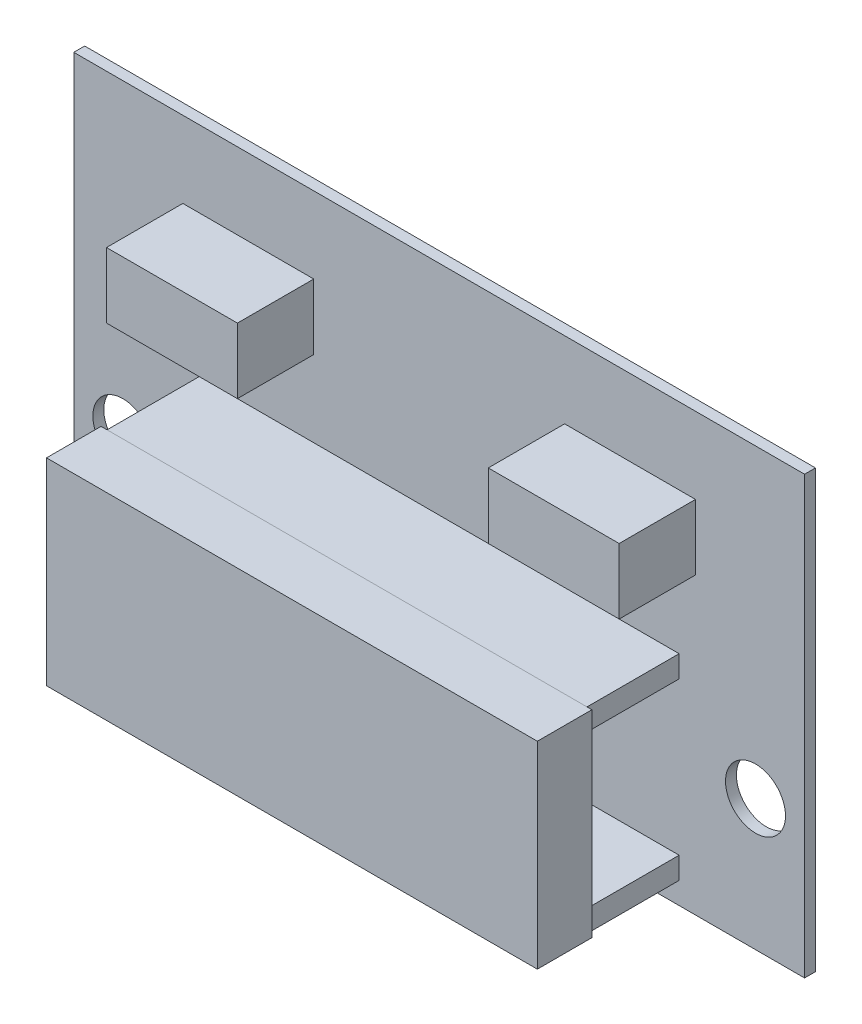
SolidWorks part; units mm, degrees
ref_plane "正面" through (0, 0, 0) normal (0, 0, 1) x (1, 0, 0)
ref_plane "平面" through (0, 0, 0) normal (0, 1, 0) x (1, 0, 0)
ref_plane "右側面" through (0, 0, 0) normal (1, 0, 0) x (0, 0, -1)
ref_plane "平面1" through (0, 0, 0) normal (0, 0, 1) x (1, 0, 0)
sketch "ｽｹｯﾁ1" plane through (0, 0, 0) normal (0, 0, 1) x (1, 0, 0)
  line L1 (-33.5, 20) -> (33.5, 20)
  line L2 (-33.5, 20) -> (-33.5, -20)
  line L3 (-33.5, -20) -> (33.5, -20)
  line L4 (33.5, 20) -> (33.5, -20)
  line L5 (-33.5, 20) -> (33.5, -20) construction
  line L6 (-33.5, -20) -> (33.5, 20) construction
  point P0 (0, 0)
  dimension "D1" = 40
  dimension "D2" = 67
extrude "ﾎﾞｽ - 押し出し1" add sketch "ｽｹｯﾁ1" along normal blind 1
sketch "ｽｹｯﾁ2" plane through (0, 0, 1) normal (0, 0, 1) x (1, 0, 0)
  line L1 (-22, 0) -> (22, 0)
  line L2 (-22, 0) -> (-22, -2)
  line L3 (-22, -2) -> (22, -2)
  line L4 (22, 0) -> (22, -2)
  line L5 (-22, 0) -> (22, -2) construction
  line L6 (-22, -2) -> (22, 0) construction
  line L7 (-22, -16) -> (22, -16)
  line L8 (-22, -16) -> (-22, -18)
  line L9 (-22, -18) -> (22, -18)
  line L10 (22, -16) -> (22, -18)
  line L11 (-22, -16) -> (22, -18) construction
  line L12 (-22, -18) -> (22, -16) construction
  point P0 (0, -1)
  point P5 (0, -17)
  dimension "D1" = 2
  dimension "D2" = 2
  dimension "D3" = 14
  dimension "D4" = 44
  dimension "D5" = 44
  dimension "D6" = 17
extrude "ﾎﾞｽ - 押し出し2" add sketch "ｽｹｯﾁ2" along normal blind 8.5
sketch "ｽｹｯﾁ3" plane through (0, 0, 9.5) normal (0, 0, 1) x (1, 0, 0)
  line L0 (22, 0) -> (-22, 0) construction
  line L1 (-22.5, 0.05) -> (22.5, 0.05)
  line L2 (-22.5, 0.05) -> (-22.5, -18.05)
  line L3 (-22.5, -18.05) -> (22.5, -18.05)
  line L4 (22.5, 0.05) -> (22.5, -18.05)
  line L5 (-22.5, 0.05) -> (22.5, -18.05) construction
  line L6 (-22.5, -18.05) -> (22.5, 0.05) construction
  point P0 (0, -9)
  dimension "D1" = 18.1
  dimension "D2" = 45
  dimension "D3" = 0.05
extrude "ﾎﾞｽ - 押し出し3" add sketch "ｽｹｯﾁ3" along normal blind 5
sketch "ｽｹｯﾁ4" plane through (0, 0, 1) normal (0, 0, 1) x (1, 0, 0)
  line L2 (-33.5, -20) -> (33.5, -20) construction
  circle A0 centre (-29, -8) radius 2.75
  circle A1 centre (29, -8) radius 2.75
  dimension "D1" = 5.5
  dimension "D2" = 5.5
  dimension "D5" = 12
  dimension "D6" = 12
  dimension "D3" = 29
  dimension "D4" = 58
extrude "ｶｯﾄ - 押し出し1" cut sketch "ｽｹｯﾁ4" against normal blind 5
sketch "ｽｹｯﾁ5" plane through (0, 0, 1) normal (0, 0, 1) x (1, 0, 0)
  line L0 (33.5, 20) -> (-33.5, 20) construction
  line L1 (-23.5, 13) -> (-11.5, 13)
  line L2 (-23.5, 13) -> (-23.5, 7)
  line L3 (-23.5, 7) -> (-11.5, 7)
  line L4 (-11.5, 13) -> (-11.5, 7)
  line L5 (-23.5, 13) -> (-11.5, 7) construction
  line L6 (-23.5, 7) -> (-11.5, 13) construction
  line L7 (-33.5, 20) -> (-33.5, -20) construction
  line L8 (0, 0) -> (0, 13.0199) construction
  line L9 (23.5, 7) -> (11.5, 7)
  line L10 (11.5, 13) -> (11.5, 7)
  line L11 (23.5, 13) -> (11.5, 13)
  line L12 (23.5, 13) -> (23.5, 7)
  point P0 (-17.5, 10)
  dimension "D1" = 10
  dimension "D2" = 12
  dimension "D3" = 6
  dimension "D4" = 10
extrude "ﾎﾞｽ - 押し出し4" add sketch "ｽｹｯﾁ5" along normal blind 7
sketch "ｽｹｯﾁ6" plane through (0, 0, 8) normal (0, 0, 1) x (1, 0, 0)
  line L0 (-11.5, 13) -> (-23.5, 13) construction
  line L1 (-5, 12) -> (-2, 12)
  line L2 (-5, 12) -> (-5, 9)
  line L3 (-5, 9) -> (-2, 9)
  line L4 (-2, 12) -> (-2, 9)
  line L5 (-5, 12) -> (-2, 9) construction
  line L6 (-5, 9) -> (-2, 12) construction
  line L7 (-1.5, 12) -> (1.5, 12)
  line L8 (-1.5, 12) -> (-1.5, 9)
  line L9 (-1.5, 9) -> (1.5, 9)
  line L10 (1.5, 12) -> (1.5, 9)
  line L11 (-1.5, 12) -> (1.5, 9) construction
  line L12 (-1.5, 9) -> (1.5, 12) construction
  line L13 (2, 12) -> (5, 12)
  line L14 (2, 12) -> (2, 9)
  line L15 (2, 9) -> (5, 9)
  line L16 (5, 12) -> (5, 9)
  line L17 (2, 12) -> (5, 9) construction
  line L18 (2, 9) -> (5, 12) construction
  line L19 (-23.5, 10) -> (-11.5, 10) construction
  line L20 (-23.5, 13) -> (-23.5, 7) construction
  line L21 (-11.5, 7) -> (-11.5, 13) construction
  line L22 (-5, 11) -> (-2, 11)
  line L23 (-2, 8) -> (-2, 11)
  line L24 (-5, 8) -> (-2, 8)
  line L25 (-5, 8) -> (-5, 11)
  line L26 (-1.5, 11) -> (1.5, 11)
  line L27 (1.5, 8) -> (1.5, 11)
  line L28 (-1.5, 8) -> (1.5, 8)
  line L29 (-1.5, 8) -> (-1.5, 11)
  line L30 (2, 11) -> (5, 11)
  line L31 (5, 8) -> (5, 11)
  line L32 (2, 8) -> (5, 8)
  line L33 (2, 8) -> (2, 11)
  point P0 (-3.5, 10.5)
  point P5 (0, 10.5)
  point P10 (3.5, 10.5)
  dimension "D1" = 2.5
  dimension "D2" = 3
  dimension "D3" = 3
  dimension "D4" = 3
  dimension "D5" = 3
  dimension "D6" = 3
  dimension "D7" = 3
  dimension "D8" = 3.5
  dimension "D9" = 3.5
